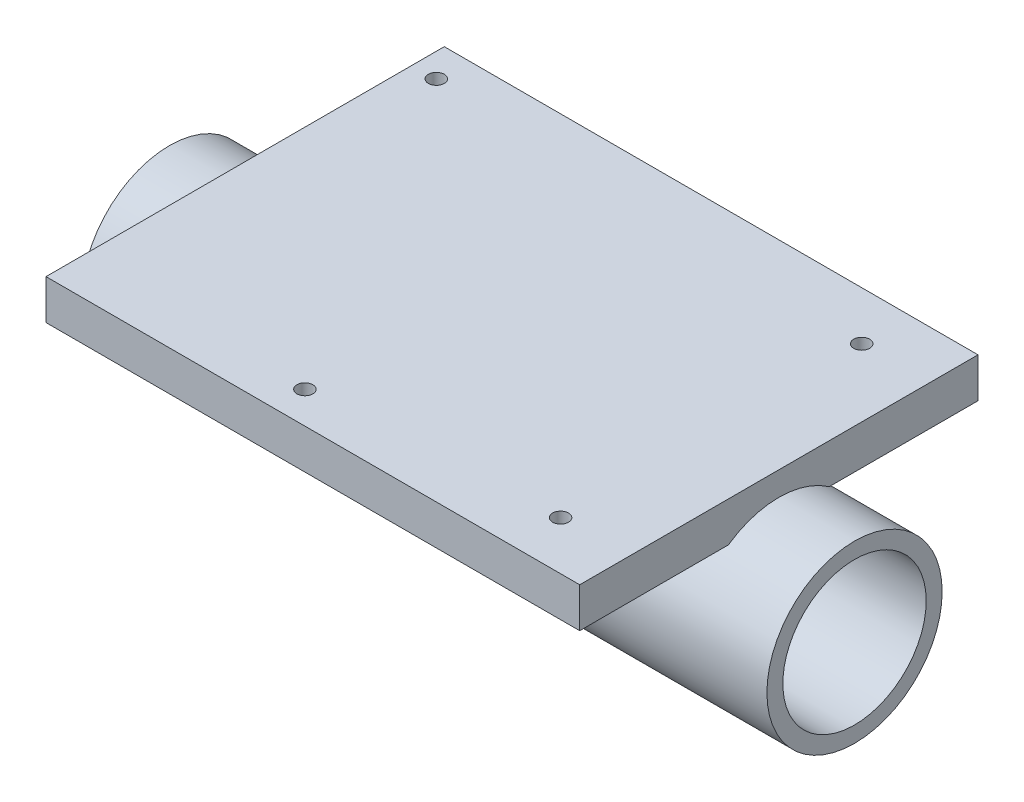
SolidWorks part; units mm, degrees
ref_plane "前视基准面" through (0, 0, 0) normal (0, 0, 1) x (1, 0, 0)
ref_plane "上视基准面" through (0, 0, 0) normal (0, 1, 0) x (1, 0, 0)
ref_plane "右视基准面" through (0, 0, 0) normal (1, 0, 0) x (0, 0, -1)
other "Configuration Table"
sketch "草图1" plane through (0, 0, 0) normal (0, 1, 0) x (1, 0, 0)
  line L1 (-33.5, -25) -> (33.5, -25)
  line L2 (-33.5, -25) -> (-33.5, 25)
  line L3 (-33.5, 25) -> (33.5, 25)
  line L4 (33.5, -25) -> (33.5, 25)
  line L5 (-33.5, -25) -> (33.5, 25) construction
  line L6 (-33.5, 25) -> (33.5, -25) construction
  point P0 (0, 0)
  dimension "D1" = 50
  dimension "D2" = 67
extrude "凸台-拉伸1" add sketch "草图1" along normal blind 5
sketch "草图2" plane through (0, 5, 0) normal (0, 1, 0) x (1, 0, 0)
  line L0 (-33.5, 25) -> (-33.5, -25) construction
  line L1 (-33.5, -25) -> (33.5, -25) construction
  line L2 (33.5, -25) -> (33.5, 25) construction
  line L3 (-2.75, 0) -> (2.75, 0) construction
  line L4 (33.5, 25) -> (-33.5, 25) construction
  circle A0 centre (-5, -21) radius 1
  circle A1 centre (25, -18.9) radius 1
  circle A2 centre (25, 18.9) radius 1
  circle A3 centre (-30.5, 21) radius 1
  dimension "D1" = 2
  dimension "D3" = 4
  dimension "D4" = 2
  dimension "D6" = 8.5
  dimension "D7" = 2
  dimension "D8" = 4
  dimension "D9" = 3
  dimension "D2" = 28.5
  dimension "D5" = 6.1
extrude "切除-拉伸1" cut sketch "草图2" against normal through all
sketch "草图4" plane through (0, 0, 0) normal (1, 0, 0) x (0, 0, -1)
  line L0 (-25, 0) -> (25, 0) construction
  circle A0 centre (0, -9) radius 11
  circle A1 centre (0, -9) radius 9
  dimension "D1" = 22
  dimension "D2" = 2
extrude "凸台-拉伸2" add sketch "草图4" along normal mid plane 86 separate body
